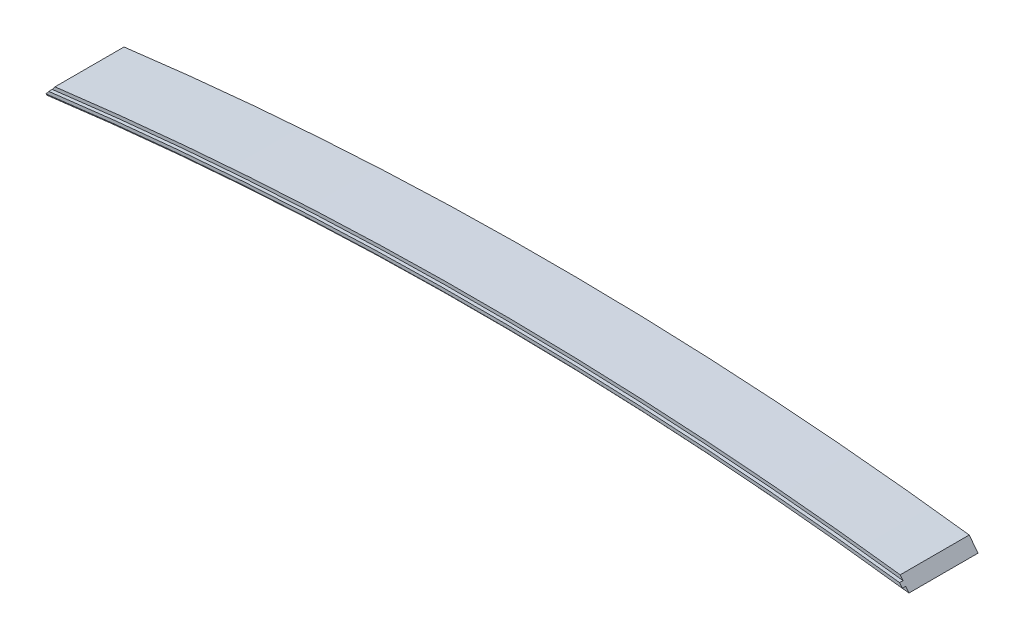
SolidWorks part; units mm, degrees
ref_plane "Front Plane" through (0, 0, 0) normal (0, 0, 1) x (1, 0, 0)
ref_plane "Top Plane" through (0, 0, 0) normal (0, 1, 0) x (1, 0, 0)
ref_plane "Right Plane" through (0, 0, 0) normal (1, 0, 0) x (0, 0, -1)
sketch "Sketch1" plane through (0, 0, 0) normal (0, 0, 1) x (1, 0, 0)
  line L0 (-635, -99.9774) -> (-622.1039, -83.1998)
  line L1 (-591.9826, -50.0244) -> (-588.4823, -79.0239) construction
  line L3 (-635, -99.9774) -> (-678.699, -105.6935) construction
  line L4 (-22.4762, -43.688) -> (-22.6762, 0) construction
  line L5 (-22.6762, 0) -> (166.2126, -2.9915) construction
  line L6 (166.2126, -2.9915) -> (357.2621, -14.2722) construction
  line L7 (357.2621, -14.2722) -> (547.1039, -44.3043) construction
  line L8 (635, -99.9774) -> (622.1039, -83.1998)
  line L9 (-22.6762, 0) -> (-211.4855, -6.2439) construction
  line L10 (-211.4855, -6.2439) -> (-402.3112, -20.833) construction
  line L11 (-402.3112, -20.833) -> (-591.9826, -50.0244) construction
  line L12 (-591.9826, -50.0244) -> (-784.7055, -161.0169) construction
  line L13 (166.2126, -2.9915) -> (164.7555, -46.4011) construction
  line L14 (357.2621, -14.2722) -> (354.2135, -56.4277) construction
  line L15 (547.1039, -44.3043) -> (543.8131, -73.8396) construction
  line L16 (635, -99.9774) -> (646.4617, -101.4767) construction
  line L17 (-635, -99.9774) -> (635, -99.9774) construction
  line L18 (-402.3112, -20.833) -> (-399.1269, -59.8829) construction
  line L19 (-211.4855, -6.2439) -> (-209.6959, -48.1157) construction
  line L20 (547.1039, -44.3043) -> (733.9355, -115.4673) construction
  line L21 (622.1039, -83.1998) -> (625.5395, -74.18) construction
  line L22 (-622.1039, -83.1998) -> (-628.9492, -71.3141) construction
  arc A0 (635, -99.9774) -> (-635, -99.9774) centre (0, -4954.4862) ccw
  arc A1 (622.1039, -83.1998) -> (-622.1039, -83.1998) centre (0, -4954.4862) ccw
  circle A2 centre (0, -4954.4862) radius 4910.8497 construction
  circle A3 centre (0, -4954.4862) radius 4895.8637 construction
  point P1 (-22.4762, -43.688)
  point P13 (-117.0808, -3.1219)
  point P20 (0, -58.6226)
  point P31 (-306.8983, -13.5384)
  point P32 (-497.1469, -35.4287)
  point P33 (71.7682, -1.4958)
  point P34 (261.7374, -8.6319)
  point P37 (452.183, -29.2883)
  dimension "D5" = 14.986
  dimension "D1" = 45
  dimension "D3" = 1270
  dimension "D2" = 41.3548
  dimension "D4" = 43.688
  dimension "D6" = 188.9125
  dimension "D7" = 380.2062
  dimension "D8" = 571.5
  dimension "D9" = 188.9125
  dimension "D10" = 380.2062
  dimension "D11" = 571.5
  dimension "D12" = 41.91
  dimension "D13" = 612.775
  dimension "D14" = 43.434
  dimension "D15" = 42.2656
  dimension "D16" = 29.718
  dimension "D17" = 45
  dimension "D18" = 9.652
  dimension "D19" = 39.1795
  dimension "D20" = 29.21
  dimension "D21" = 13.716
extrude "Boss-Extrude1" add sketch "Sketch1" along normal blind 101.6
sketch "Sketch2" plane through (0, 0, 101.6) normal (0, 0, 1) x (1, 0, 0)
  line L0 (-622.1039, -83.1998) -> (-635, -99.9774) construction
  line L1 (-626.2089, -88.5404) -> (-630.2523, -93.8007)
  line L2 (635, -99.9774) -> (622.1039, -83.1998) construction
  line L3 (630.2523, -93.8007) -> (626.2089, -88.5404)
  arc A2 (635.7149, -94.5122) -> (-635.7149, -94.5122) centre (0, -4954.4862) ccw
  arc A3 (630.2523, -93.8007) -> (-630.2523, -93.8007) centre (0, -4954.4862) ccw
  arc A6 (626.2089, -88.5404) -> (-626.2089, -88.5404) centre (0, -4954.4862) ccw
  dimension "D2" = 4.699
  dimension "D1" = 5.5118
extrude "Boss-Extrude2" add sketch "Sketch2" along normal blind 5.08
